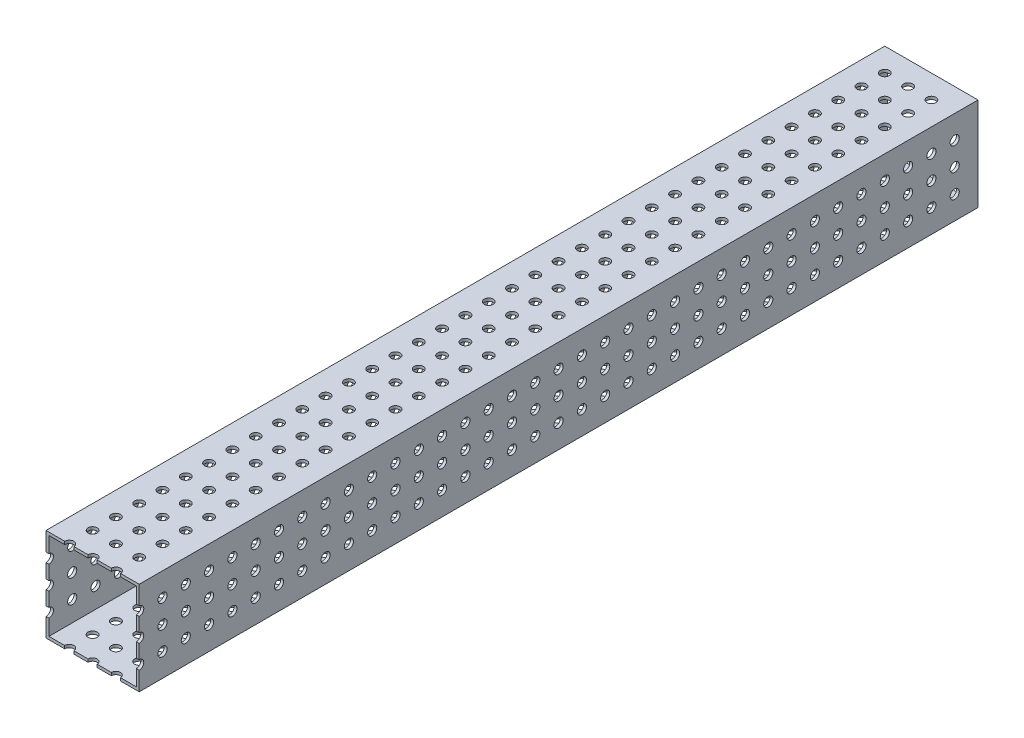
SolidWorks part; units mm, degrees
ref_plane "Front Plane" through (0, 0, 0) normal (0, 0, 1) x (1, 0, 0)
ref_plane "Top Plane" through (0, 0, 0) normal (0, 1, 0) x (1, 0, 0)
ref_plane "Right Plane" through (0, 0, 0) normal (1, 0, 0) x (0, 0, -1)
sketch "Sketch1" plane through (0, 0, 0) normal (0, 0, 1) x (1, 0, 0)
  line L0 (1.5875, 1.5875) -> (49.2125, 1.5875)
  line L1 (0, 0) -> (50.8, 0)
  line L2 (0, 0) -> (0, 50.8)
  line L3 (0, 50.8) -> (50.8, 50.8)
  line L4 (50.8, 0) -> (50.8, 50.8)
  line L5 (49.2125, 1.5875) -> (49.2125, 49.2125)
  line L6 (1.5875, 49.2125) -> (49.2125, 49.2125)
  line L7 (1.5875, 1.5875) -> (1.5875, 49.2125)
  dimension "D1" = 50.8
  dimension "D2" = 1.5875
extrude "Boss-Extrude1" add sketch "Sketch1" along normal blind 457.2
sketch "Sketch2" plane through (0, 50.8, 0) normal (0, 1, 0) x (1, 0, 0)
  line L0 (50.8, 0) -> (0, 0) construction
  line L1 (0, -457.2) -> (0, 0) construction
  line L2 (12.7, -12.7) -> (25.4, -12.7) construction
  line L3 (12.7, -12.7) -> (12.7, -25.4) construction
  circle A0 centre (12.7, -12.7) radius 2.4892
  circle A1 centre (25.4, -12.7) radius 2.4892
  circle A2 centre (38.1, -12.7) radius 2.4892
  circle A3 centre (25.4, -25.4) radius 2.4892
  circle A4 centre (38.1, -25.4) radius 2.4892
  circle A5 centre (25.4, -38.1) radius 2.4892
  circle A6 centre (38.1, -38.1) radius 2.4892
  circle A7 centre (25.4, -50.8) radius 2.4892
  circle A8 centre (38.1, -50.8) radius 2.4892
  circle A9 centre (25.4, -63.5) radius 2.4892
  circle A10 centre (38.1, -63.5) radius 2.4892
  circle A11 centre (25.4, -76.2) radius 2.4892
  circle A12 centre (38.1, -76.2) radius 2.4892
  circle A13 centre (25.4, -88.9) radius 2.4892
  circle A14 centre (38.1, -88.9) radius 2.4892
  circle A15 centre (25.4, -101.6) radius 2.4892
  circle A16 centre (38.1, -101.6) radius 2.4892
  circle A17 centre (25.4, -114.3) radius 2.4892
  circle A18 centre (38.1, -114.3) radius 2.4892
  circle A19 centre (25.4, -127) radius 2.4892
  circle A20 centre (38.1, -127) radius 2.4892
  circle A21 centre (25.4, -139.7) radius 2.4892
  circle A22 centre (38.1, -139.7) radius 2.4892
  circle A23 centre (25.4, -152.4) radius 2.4892
  circle A24 centre (38.1, -152.4) radius 2.4892
  circle A25 centre (25.4, -165.1) radius 2.4892
  circle A26 centre (38.1, -165.1) radius 2.4892
  circle A27 centre (25.4, -177.8) radius 2.4892
  circle A28 centre (38.1, -177.8) radius 2.4892
  circle A29 centre (25.4, -190.5) radius 2.4892
  circle A30 centre (38.1, -190.5) radius 2.4892
  circle A31 centre (25.4, -203.2) radius 2.4892
  circle A32 centre (38.1, -203.2) radius 2.4892
  circle A33 centre (25.4, -215.9) radius 2.4892
  circle A34 centre (38.1, -215.9) radius 2.4892
  circle A35 centre (25.4, -228.6) radius 2.4892
  circle A36 centre (38.1, -228.6) radius 2.4892
  circle A37 centre (25.4, -241.3) radius 2.4892
  circle A38 centre (38.1, -241.3) radius 2.4892
  circle A39 centre (25.4, -254) radius 2.4892
  circle A40 centre (38.1, -254) radius 2.4892
  circle A41 centre (25.4, -266.7) radius 2.4892
  circle A42 centre (38.1, -266.7) radius 2.4892
  circle A43 centre (25.4, -279.4) radius 2.4892
  circle A44 centre (38.1, -279.4) radius 2.4892
  circle A45 centre (25.4, -292.1) radius 2.4892
  circle A46 centre (38.1, -292.1) radius 2.4892
  circle A47 centre (25.4, -304.8) radius 2.4892
  circle A48 centre (38.1, -304.8) radius 2.4892
  circle A49 centre (25.4, -317.5) radius 2.4892
  circle A50 centre (38.1, -317.5) radius 2.4892
  circle A51 centre (25.4, -330.2) radius 2.4892
  circle A52 centre (38.1, -330.2) radius 2.4892
  circle A53 centre (25.4, -342.9) radius 2.4892
  circle A54 centre (38.1, -342.9) radius 2.4892
  circle A55 centre (25.4, -355.6) radius 2.4892
  circle A56 centre (38.1, -355.6) radius 2.4892
  circle A57 centre (25.4, -368.3) radius 2.4892
  circle A58 centre (38.1, -368.3) radius 2.4892
  circle A59 centre (25.4, -381) radius 2.4892
  circle A60 centre (38.1, -381) radius 2.4892
  circle A61 centre (25.4, -393.7) radius 2.4892
  circle A62 centre (38.1, -393.7) radius 2.4892
  circle A63 centre (25.4, -406.4) radius 2.4892
  circle A64 centre (38.1, -406.4) radius 2.4892
  circle A65 centre (25.4, -419.1) radius 2.4892
  circle A66 centre (38.1, -419.1) radius 2.4892
  circle A67 centre (25.4, -431.8) radius 2.4892
  circle A68 centre (38.1, -431.8) radius 2.4892
  circle A69 centre (25.4, -444.5) radius 2.4892
  circle A70 centre (38.1, -444.5) radius 2.4892
  circle A71 centre (25.4, -457.2) radius 2.4892
  circle A72 centre (38.1, -457.2) radius 2.4892
  circle A73 centre (12.7, -25.4) radius 2.4892
  circle A74 centre (12.7, -38.1) radius 2.4892
  circle A75 centre (12.7, -50.8) radius 2.4892
  circle A76 centre (12.7, -63.5) radius 2.4892
  circle A77 centre (12.7, -76.2) radius 2.4892
  circle A78 centre (12.7, -88.9) radius 2.4892
  circle A79 centre (12.7, -101.6) radius 2.4892
  circle A80 centre (12.7, -114.3) radius 2.4892
  circle A81 centre (12.7, -127) radius 2.4892
  circle A82 centre (12.7, -139.7) radius 2.4892
  circle A83 centre (12.7, -152.4) radius 2.4892
  circle A84 centre (12.7, -165.1) radius 2.4892
  circle A85 centre (12.7, -177.8) radius 2.4892
  circle A86 centre (12.7, -190.5) radius 2.4892
  circle A87 centre (12.7, -203.2) radius 2.4892
  circle A88 centre (12.7, -215.9) radius 2.4892
  circle A89 centre (12.7, -228.6) radius 2.4892
  circle A90 centre (12.7, -241.3) radius 2.4892
  circle A91 centre (12.7, -254) radius 2.4892
  circle A92 centre (12.7, -266.7) radius 2.4892
  circle A93 centre (12.7, -279.4) radius 2.4892
  circle A94 centre (12.7, -292.1) radius 2.4892
  circle A95 centre (12.7, -304.8) radius 2.4892
  circle A96 centre (12.7, -317.5) radius 2.4892
  circle A97 centre (12.7, -330.2) radius 2.4892
  circle A98 centre (12.7, -342.9) radius 2.4892
  circle A99 centre (12.7, -355.6) radius 2.4892
  circle A100 centre (12.7, -368.3) radius 2.4892
  circle A101 centre (12.7, -381) radius 2.4892
  circle A102 centre (12.7, -393.7) radius 2.4892
  circle A103 centre (12.7, -406.4) radius 2.4892
  circle A104 centre (12.7, -419.1) radius 2.4892
  circle A105 centre (12.7, -431.8) radius 2.4892
  circle A106 centre (12.7, -444.5) radius 2.4892
  circle A107 centre (12.7, -457.2) radius 2.4892
  dimension "D1" = 4.9784
  dimension "D2" = 12.7
  dimension "D3" = 12.7
  dimension "D6" = 90
  dimension "D7" = 12.7
  dimension "D8" = 12.7
  dimension "D4" = 3
  dimension "D5" = 36
extrude "Cut-Extrude1" cut sketch "Sketch2" against normal through all
sketch "Sketch3" plane through (0, 0, 0) normal (-1, 0, 0) x (0, 0, 1)
  line L0 (0, 50.8) -> (0, 0) construction
  line L1 (457.2, 50.8) -> (0, 50.8) construction
  line L2 (12.7, 38.1) -> (25.4, 38.1) construction
  line L3 (12.7, 38.1) -> (12.7, 25.4) construction
  circle A0 centre (12.7, 38.1) radius 2.4892
  circle A1 centre (25.4, 38.1) radius 2.4892
  circle A2 centre (38.1, 38.1) radius 2.4892
  circle A3 centre (50.8, 38.1) radius 2.4892
  circle A4 centre (63.5, 38.1) radius 2.4892
  circle A5 centre (76.2, 38.1) radius 2.4892
  circle A6 centre (88.9, 38.1) radius 2.4892
  circle A7 centre (101.6, 38.1) radius 2.4892
  circle A8 centre (114.3, 38.1) radius 2.4892
  circle A9 centre (127, 38.1) radius 2.4892
  circle A10 centre (139.7, 38.1) radius 2.4892
  circle A11 centre (152.4, 38.1) radius 2.4892
  circle A12 centre (165.1, 38.1) radius 2.4892
  circle A13 centre (177.8, 38.1) radius 2.4892
  circle A14 centre (190.5, 38.1) radius 2.4892
  circle A15 centre (203.2, 38.1) radius 2.4892
  circle A16 centre (215.9, 38.1) radius 2.4892
  circle A17 centre (228.6, 38.1) radius 2.4892
  circle A18 centre (241.3, 38.1) radius 2.4892
  circle A19 centre (254, 38.1) radius 2.4892
  circle A20 centre (266.7, 38.1) radius 2.4892
  circle A21 centre (279.4, 38.1) radius 2.4892
  circle A22 centre (292.1, 38.1) radius 2.4892
  circle A23 centre (304.8, 38.1) radius 2.4892
  circle A24 centre (317.5, 38.1) radius 2.4892
  circle A25 centre (330.2, 38.1) radius 2.4892
  circle A26 centre (342.9, 38.1) radius 2.4892
  circle A27 centre (355.6, 38.1) radius 2.4892
  circle A28 centre (368.3, 38.1) radius 2.4892
  circle A29 centre (381, 38.1) radius 2.4892
  circle A30 centre (393.7, 38.1) radius 2.4892
  circle A31 centre (406.4, 38.1) radius 2.4892
  circle A32 centre (419.1, 38.1) radius 2.4892
  circle A33 centre (431.8, 38.1) radius 2.4892
  circle A34 centre (444.5, 38.1) radius 2.4892
  circle A35 centre (457.2, 38.1) radius 2.4892
  circle A36 centre (25.4, 25.4) radius 2.4892
  circle A37 centre (38.1, 25.4) radius 2.4892
  circle A38 centre (50.8, 25.4) radius 2.4892
  circle A39 centre (63.5, 25.4) radius 2.4892
  circle A40 centre (76.2, 25.4) radius 2.4892
  circle A41 centre (88.9, 25.4) radius 2.4892
  circle A42 centre (101.6, 25.4) radius 2.4892
  circle A43 centre (114.3, 25.4) radius 2.4892
  circle A44 centre (127, 25.4) radius 2.4892
  circle A45 centre (139.7, 25.4) radius 2.4892
  circle A46 centre (152.4, 25.4) radius 2.4892
  circle A47 centre (165.1, 25.4) radius 2.4892
  circle A48 centre (177.8, 25.4) radius 2.4892
  circle A49 centre (190.5, 25.4) radius 2.4892
  circle A50 centre (203.2, 25.4) radius 2.4892
  circle A51 centre (215.9, 25.4) radius 2.4892
  circle A52 centre (228.6, 25.4) radius 2.4892
  circle A53 centre (241.3, 25.4) radius 2.4892
  circle A54 centre (254, 25.4) radius 2.4892
  circle A55 centre (266.7, 25.4) radius 2.4892
  circle A56 centre (279.4, 25.4) radius 2.4892
  circle A57 centre (292.1, 25.4) radius 2.4892
  circle A58 centre (304.8, 25.4) radius 2.4892
  circle A59 centre (317.5, 25.4) radius 2.4892
  circle A60 centre (330.2, 25.4) radius 2.4892
  circle A61 centre (342.9, 25.4) radius 2.4892
  circle A62 centre (355.6, 25.4) radius 2.4892
  circle A63 centre (368.3, 25.4) radius 2.4892
  circle A64 centre (381, 25.4) radius 2.4892
  circle A65 centre (393.7, 25.4) radius 2.4892
  circle A66 centre (406.4, 25.4) radius 2.4892
  circle A67 centre (419.1, 25.4) radius 2.4892
  circle A68 centre (431.8, 25.4) radius 2.4892
  circle A69 centre (444.5, 25.4) radius 2.4892
  circle A70 centre (457.2, 25.4) radius 2.4892
  circle A71 centre (25.4, 12.7) radius 2.4892
  circle A72 centre (38.1, 12.7) radius 2.4892
  circle A73 centre (50.8, 12.7) radius 2.4892
  circle A74 centre (63.5, 12.7) radius 2.4892
  circle A75 centre (76.2, 12.7) radius 2.4892
  circle A76 centre (88.9, 12.7) radius 2.4892
  circle A77 centre (101.6, 12.7) radius 2.4892
  circle A78 centre (114.3, 12.7) radius 2.4892
  circle A79 centre (127, 12.7) radius 2.4892
  circle A80 centre (139.7, 12.7) radius 2.4892
  circle A81 centre (152.4, 12.7) radius 2.4892
  circle A82 centre (165.1, 12.7) radius 2.4892
  circle A83 centre (177.8, 12.7) radius 2.4892
  circle A84 centre (190.5, 12.7) radius 2.4892
  circle A85 centre (203.2, 12.7) radius 2.4892
  circle A86 centre (215.9, 12.7) radius 2.4892
  circle A87 centre (228.6, 12.7) radius 2.4892
  circle A88 centre (241.3, 12.7) radius 2.4892
  circle A89 centre (254, 12.7) radius 2.4892
  circle A90 centre (266.7, 12.7) radius 2.4892
  circle A91 centre (279.4, 12.7) radius 2.4892
  circle A92 centre (292.1, 12.7) radius 2.4892
  circle A93 centre (304.8, 12.7) radius 2.4892
  circle A94 centre (317.5, 12.7) radius 2.4892
  circle A95 centre (330.2, 12.7) radius 2.4892
  circle A96 centre (342.9, 12.7) radius 2.4892
  circle A97 centre (355.6, 12.7) radius 2.4892
  circle A98 centre (368.3, 12.7) radius 2.4892
  circle A99 centre (381, 12.7) radius 2.4892
  circle A100 centre (393.7, 12.7) radius 2.4892
  circle A101 centre (406.4, 12.7) radius 2.4892
  circle A102 centre (419.1, 12.7) radius 2.4892
  circle A103 centre (431.8, 12.7) radius 2.4892
  circle A104 centre (444.5, 12.7) radius 2.4892
  circle A105 centre (457.2, 12.7) radius 2.4892
  circle A106 centre (12.7, 25.4) radius 2.4892
  circle A107 centre (12.7, 12.7) radius 2.4892
  dimension "D1" = 4.9784
  dimension "D2" = 12.7
  dimension "D3" = 12.7
  dimension "D6" = 90
  dimension "D7" = 12.7
  dimension "D8" = 12.7
  dimension "D4" = 36
  dimension "D5" = 3
extrude "Cut-Extrude2" cut sketch "Sketch3" against normal through all
